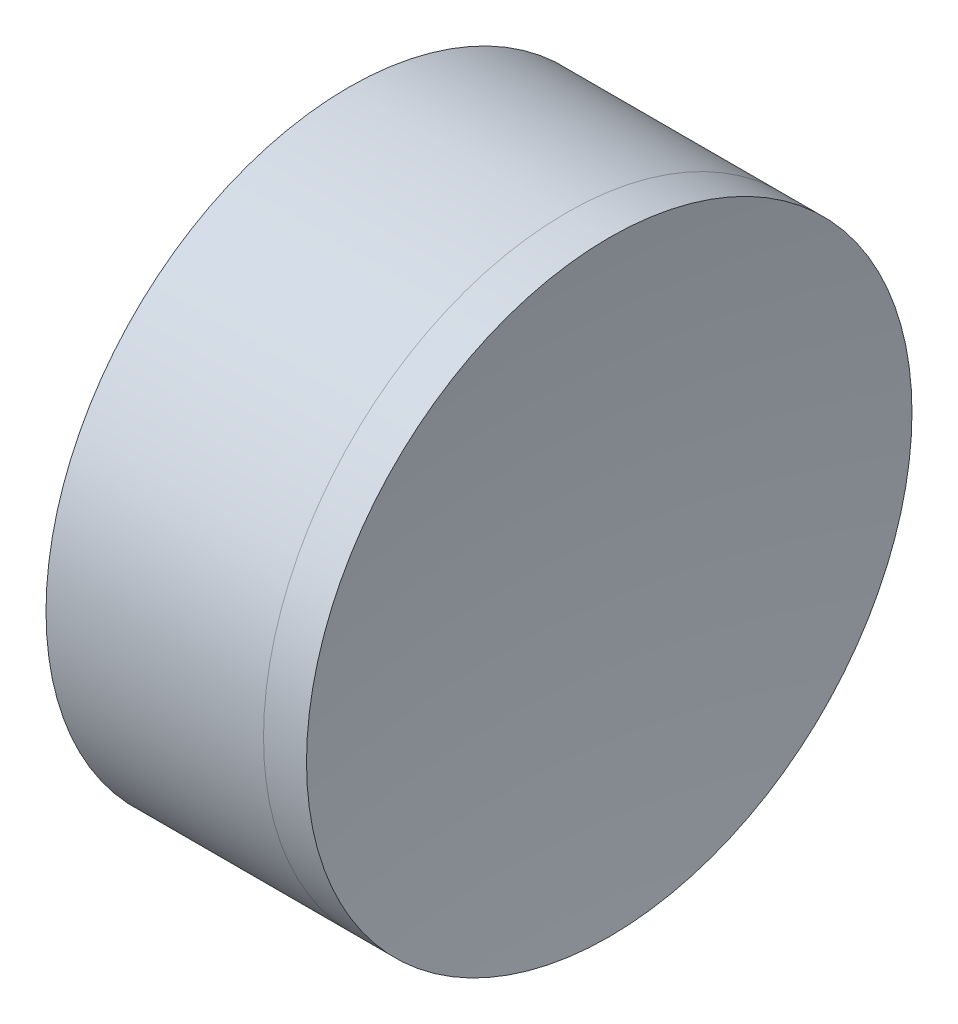
SolidWorks part; units mm, degrees
ref_plane "前视基准面" through (0, 0, 0) normal (0, 0, 1) x (1, 0, 0)
ref_plane "上视基准面" through (0, 0, 0) normal (0, 1, 0) x (1, 0, 0)
ref_plane "右视基准面" through (0, 0, 0) normal (1, 0, 0) x (0, 0, -1)
sketch "草图1" plane through (0, 0, 0) normal (0, 1, 0) x (1, 0, 0)
  line L0 (-0.8161, 0) -> (399.8689, 0) construction
  line L1 (228.102, 12.5) -> (237.0829, 12.5)
  line L4 (228.102, -12.5) -> (237.0829, -12.5)
  arc A0 (228.102, -12.5) -> (228.102, 12.5) centre (199.5264, 0) ccw
  arc A1 (237.0829, 12.5) -> (237.0829, -12.5) centre (258.6064, 0) ccw
  point P6 (230.7164, 0)
  point P8 (233.7164, 0)
  dimension "D3" = 12.5
  dimension "D4" = 3
  dimension "D1" = 31.19
  dimension "D5" = 24.89
  dimension "D2" = 12.5
revolve "旋转1" add sketch "草图1" angle 360 about L0
sketch "草图2" plane through (0, 0, 0) normal (0, 1, 0) x (1, 0, 0)
  line L2 (228.102, 0) -> (249.4445, 0) construction
  line L3 (228.102, -12.5) -> (228.102, 12.5) construction
  line L6 (237.0829, 12.5) -> (238.8572, 12.5)
  line L7 (237.0829, -12.5) -> (238.8572, -12.5)
  arc A2 (237.0829, 12.5) -> (237.0829, -12.5) centre (258.6064, 0) ccw construction
  arc A3 (237.0829, 12.5) -> (237.0829, -12.5) centre (258.6064, 0) ccw
  arc A4 (238.8572, 12.5) -> (238.8572, -12.5) centre (323.2464, 0) ccw
  point P8 (233.7164, 0)
  point P9 (237.9364, 0)
  dimension "D1" = 4.22
  dimension "D2" = 85.31
revolve "旋转3" add sketch "草图2" angle 360 about L2
